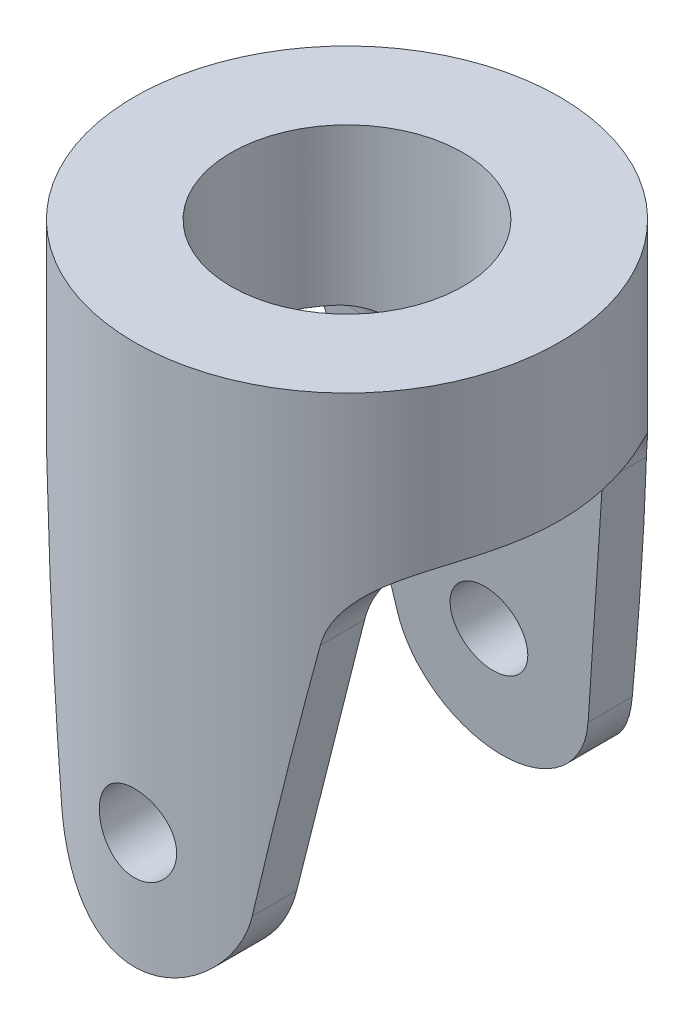
SolidWorks part; units mm, degrees
ref_plane "Front Plane" through (0, 0, 0) normal (0, 0, 1) x (1, 0, 0)
ref_plane "Top Plane" through (0, 0, 0) normal (0, 1, 0) x (1, 0, 0)
ref_plane "Right Plane" through (0, 0, 0) normal (1, 0, 0) x (0, 0, -1)
sketch "Sketch1" plane through (0, 0, 0) normal (0, 1, 0) x (1, 0, 0)
  circle A0 centre (0, 0) radius 5.5
  dimension "D1" = 11
extrude "Boss-Extrude1" add sketch "Sketch1" along normal blind 14
sketch "Sketch3" plane through (0, 0, 0) normal (0, 0, 1) x (1, 0, 0)
  line L0 (5.5, 0) -> (5.5, 14) construction
  line L1 (3.5283, 8.3353) -> (2.4646, 2.0808)
  line L2 (-2.4646, 2.0808) -> (-3.5283, 8.3353)
  line L3 (-5.5, 14) -> (-5.5, 0) construction
  line L4 (5.5, 14) -> (-5.5, 14) construction
  arc A0 (5.5, 10) -> (3.5283, 8.3353) centre (5.5, 8) ccw
  arc A1 (2.4646, 2.0808) -> (-2.4646, 2.0808) centre (0, 2.5) cw
  arc A2 (-5.5, 10) -> (-3.5283, 8.3353) centre (-5.5, 8) cw
  dimension "D3" = 2.5
  dimension "D1" = 4
  dimension "D2" = 6
extrude "Cut-Extrude3" cut sketch "Sketch3" against normal through all both and the other way through all flip side to cut
sketch "Sketch4" plane through (0, 0, 0) normal (1, 0, 0) x (0, 0, -1)
  line L0 (4.0048, 0) -> (-3.9952, 0)
  line L1 (-5.5, 0) -> (5.5, 0) construction
  line L2 (-3.9952, 0) -> (-2.9891, 9.0748)
  line L3 (2.9987, 9.0748) -> (4.0048, 0)
  line L4 (2.0048, 9.9646) -> (-1.9952, 9.9646)
  arc A1 (2.9987, 9.0748) -> (2.0048, 9.9646) centre (2.0048, 8.9646) ccw
  arc A2 (-1.9952, 9.9646) -> (-2.9891, 9.0748) centre (-1.9952, 8.9646) ccw
  spline S1 degree 3 poles (-4.2191, 8.3353) (-4.203, 8.4488) (-4.179, 8.5573) (-4.1157, 8.7649) (-4.0757, 8.8651) (-3.9352, 9.1423) (-3.8124, 9.2992) (-3.5273, 9.5507) (-3.3634, 9.6478) (-3.0093, 9.7964) (-2.8211, 9.848) (-2.4243, 9.924) (-2.2155, 9.948) (-1.7921, 9.9799) (-1.5759, 9.988) (-1.1349, 9.9976) (-0.9088, 9.9989) (-0.454, 10.0002) (0.0005, 9.9998) (0.4548, 10.0002) (0.9089, 9.9989) (1.1355, 9.9976) (1.7963, 9.9832) (2.218, 9.963) (2.8186, 9.8487) (3.0079, 9.7969) (3.3619, 9.6486) (3.5266, 9.5512) (3.8117, 9.3) (3.9348, 9.1427) (4.0749, 8.8667) (4.1152, 8.7664) (4.1789, 8.5577) (4.203, 8.4489) (4.2191, 8.3353) knots 0 0 0 0 0.03125 0.03125 0.0625 0.0625 0.125 0.125 0.1875 0.1875 0.25 0.25 0.3125 0.3125 0.375 0.375 0.4375 0.4375 0.5 0.5625 0.5625 0.625 0.625 0.75 0.75 0.8125 0.8125 0.875 0.875 0.9375 0.9375 0.96875 0.96875 1 1 1 1 construction
  dimension "D1" = 8
  dimension "D3" = 1
  dimension "D2" = 4
extrude "Cut-Extrude4" cut sketch "Sketch4" against normal through all both and the other way through all
sketch "Sketch5" plane through (0, 0, 0) normal (0, 1, 0) x (1, 0, 0)
  circle A0 centre (0, 0) radius 3
  dimension "D1" = 6
extrude "Cut-Extrude7" cut sketch "Sketch5" against normal blind 14 and the other way through all
sketch "Sketch6" plane through (0, 0, 0) normal (0, 0, 1) x (1, 0, 0)
  line L0 (5.5, 14) -> (-5.5, 14) construction
  circle A0 centre (0, 3) radius 1
  dimension "D1" = 2
  dimension "D2" = 11
extrude "Cut-Extrude8" cut sketch "Sketch6" against normal through all both and the other way through all
